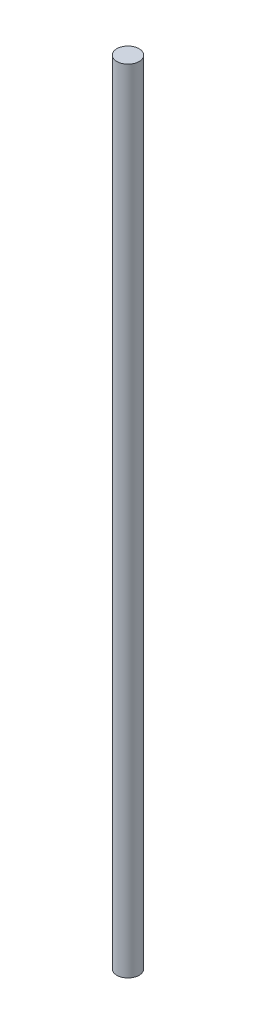
SolidWorks part; units mm, degrees
ref_plane "Front Plane" through (0, 0, 0) normal (0, 0, 1) x (1, 0, 0)
ref_plane "Top Plane" through (0, 0, 0) normal (0, 1, 0) x (1, 0, 0)
ref_plane "Right Plane" through (0, 0, 0) normal (1, 0, 0) x (0, 0, -1)
sketch "Sketch1" plane through (0, 0, 0) normal (0, 1, 0) x (1, 0, 0)
  circle A0 centre (0, 0) radius 2.5
  dimension "D1" = 5
extrude "Boss-Extrude1" add sketch "Sketch1" along normal blind 177.8
